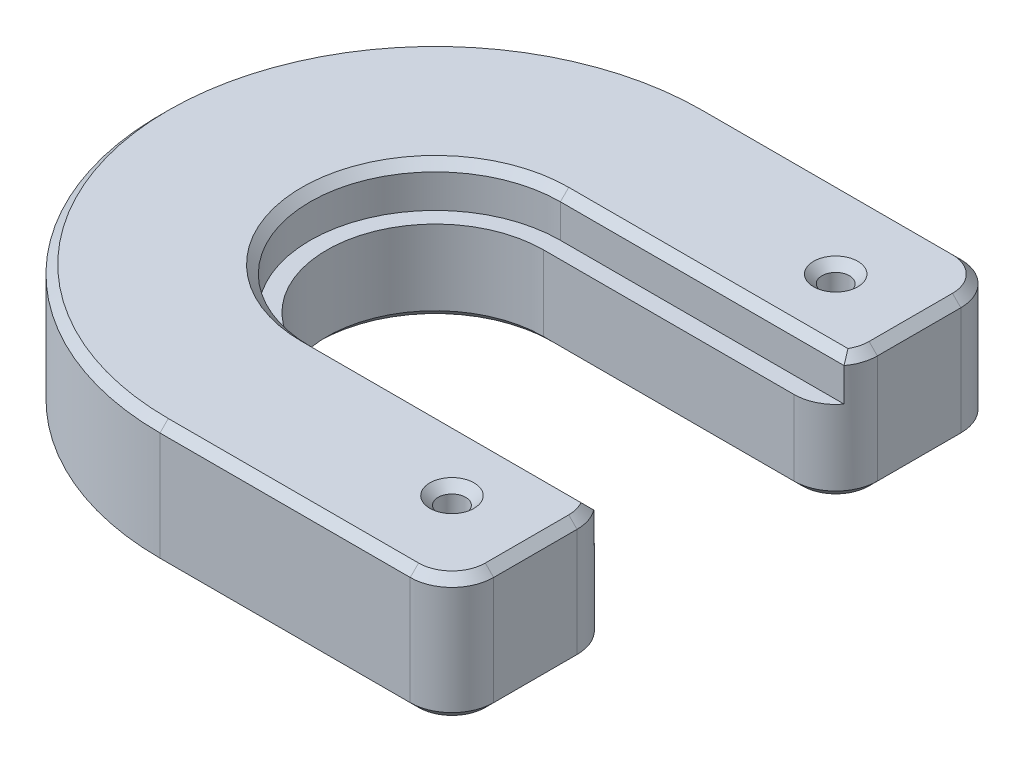
SolidWorks part; units mm, degrees
material "PLA"
ref_plane "Front Plane" through (0, 0, 0) normal (0, 0, 1) x (1, 0, 0)
ref_plane "Top Plane" through (0, 0, 0) normal (0, 1, 0) x (1, 0, 0)
ref_plane "Right Plane" through (0, 0, 0) normal (1, 0, 0) x (0, 0, -1)
sketch "Sketch1" plane through (0, 0, 0) normal (0, 1, 0) x (1, 0, 0)
  line L0 (0, 33) -> (35, 33)
  line L2 (35, -33) -> (0, -33)
  line L3 (0, 13) -> (35, 13)
  line L4 (35, 33) -> (35, 13)
  line L5 (0, -13) -> (35, -13)
  line L6 (35, -13) -> (35, -33)
  arc A0 (0, 13) -> (0, -13) centre (0, 0) ccw
  arc A1 (0, 33) -> (0, -33) centre (0, 0) ccw
  circle A2 centre (0, 0) radius 33 construction
  circle A3 centre (0, 0) radius 13 construction
  dimension "D1" = 26
  dimension "D3" = 35
  dimension "D4" = 35
  dimension "D2" = 20
extrude "Boss-Extrude1" add sketch "Sketch1" along normal blind 10
sketch "Sketch4" plane through (0, 10, 0) normal (0, 1, 0) x (1, 0, 0)
  line L0 (0, 15) -> (35, 15)
  line L1 (0, -15) -> (35, -15)
  line L6 (35, 13) -> (35, 33)
  line L7 (35, 33) -> (0, 33)
  line L8 (0, -33) -> (35, -33)
  line L9 (35, -33) -> (35, -13)
  line L10 (35, -13) -> (0, -13)
  line L11 (0, 13) -> (35, 13)
  line L12 (35, 15) -> (35, 33)
  line L13 (35, 33) -> (0, 33)
  line L14 (0, -33) -> (35, -33)
  line L15 (35, -33) -> (35, -15)
  arc A2 (0, 15) -> (0, -15) centre (0, 0) ccw
  arc A5 (0, 33) -> (0, -33) centre (0, 0) ccw
  arc A6 (0, 13) -> (0, -13) centre (0, 0) ccw
  arc A7 (0, 33) -> (0, -33) centre (0, 0) ccw
  dimension "D2" = 0
extrude "Boss-Extrude3" add sketch "Sketch4" along normal blind 5
fillet "Fillet1" radius 5 4 edges at (35, 7.5, -33) (35, 5, -13) (35, 5, 13) (35, 7.5, 33)
sketch "Sketch5" plane through (0, 15, 0) normal (0, 1, 0) x (1, 0, 0)
  line L0 (30, 13) -> (30, 33) construction
  line L1 (35, 23) -> (25, 23) construction
  line L2 (35, 18) -> (35, 28) construction
  line L3 (25, 23) -> (35, -23) construction
  line L4 (35, -28) -> (35, -18) construction
  line L5 (35, -23) -> (25, -23) construction
  arc A0 (35, 28) -> (30, 33) centre (30, 28) ccw construction
  circle A1 centre (25, 23) radius 1.65
  circle A2 centre (25, -23) radius 1.65
  point P17 (0, 0)
  dimension "D1" = 3.3
  dimension "D2" = 10
extrude "Cut-Extrude2" cut sketch "Sketch5" against normal blind 20
chamfer "Chamfer1" distance 1 angle 45 28 edges at (25, 15, 24.65) (25, 0, 24.65) (25, 15, -21.35) (25, 0, -21.35) (35, 0, 23) (33.5355, 0, 14.4645) (33.5355, 0, 31.5355) (15, 0, 13) (15, 0, 33) (-13, 0, 0) (-33, 0, 0) (15, 0, -13) (15, 0, -33) (33.5355, 0, -14.4645) (33.5355, 0, -31.5355) (35, 0, -23) (17, 15, -15) (-15, 15, 0) (17, 15, 15) (34.7434, 15, -16.4189) (35, 15, -23) (33.5355, 15, -31.5355) (34.7434, 15, 16.4189) (15, 15, -33) (35, 15, 23) (-33, 15, 0) (33.5355, 15, 31.5355) (15, 15, 33)
